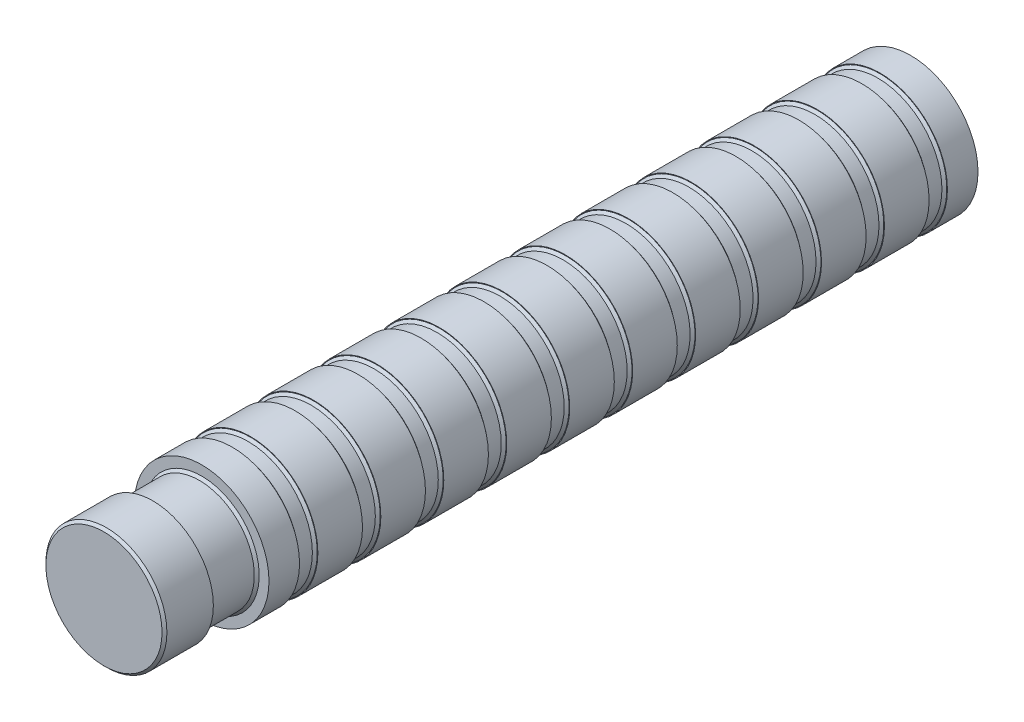
SolidWorks part; units mm, degrees
ref_plane "Front Plane" through (0, 0, 0) normal (0, 0, 1) x (1, 0, 0)
ref_plane "Top Plane" through (0, 0, 0) normal (0, 1, 0) x (1, 0, 0)
ref_plane "Right Plane" through (0, 0, 0) normal (1, 0, 0) x (0, 0, -1)
sketch "Sketch2" plane through (0, 0, 0) normal (1, 0, 0) x (0, 0, -1)
  line L0 (-29, 0) -> (29, 0)
  line L2 (-29, 5.5) -> (-26.5, 5.5)
  line L3 (29, 5.5) -> (29, 0)
  line L4 (-26.5, 5.5) -> (-26.5, 5.25)
  line L5 (-26.5, 5.25) -> (-25, 5.25)
  line L6 (-25, 5.25) -> (-25, 5.5)
  line L7 (-21.35, 5.5) -> (-21.35, 5.25)
  line L8 (-21.35, 5.25) -> (-19.85, 5.25)
  line L9 (-19.85, 5.25) -> (-19.85, 5.5)
  line L10 (-16.2, 5.5) -> (-16.2, 5.25)
  line L11 (-16.2, 5.25) -> (-14.7, 5.25)
  line L12 (-14.7, 5.25) -> (-14.7, 5.5)
  line L13 (-11.05, 5.5) -> (-11.05, 5.25)
  line L14 (-11.05, 5.25) -> (-9.55, 5.25)
  line L15 (-9.55, 5.25) -> (-9.55, 5.5)
  line L16 (-5.9, 5.5) -> (-5.9, 5.25)
  line L17 (-5.9, 5.25) -> (-4.4, 5.25)
  line L18 (-4.4, 5.25) -> (-4.4, 5.5)
  line L19 (-0.75, 5.5) -> (-0.75, 5.25)
  line L20 (-0.75, 5.25) -> (0.75, 5.25)
  line L21 (0.75, 5.25) -> (0.75, 5.5)
  line L22 (4.4, 5.5) -> (4.4, 5.25)
  line L23 (4.4, 5.25) -> (5.9, 5.25)
  line L24 (5.9, 5.25) -> (5.9, 5.5)
  line L25 (9.55, 5.5) -> (9.55, 5.25)
  line L26 (9.55, 5.25) -> (11.05, 5.25)
  line L27 (11.05, 5.25) -> (11.05, 5.5)
  line L28 (14.7, 5.5) -> (14.7, 5.25)
  line L29 (14.7, 5.25) -> (16.2, 5.25)
  line L30 (16.2, 5.25) -> (16.2, 5.5)
  line L31 (-25, 5.5) -> (-21.35, 5.5)
  line L32 (-19.85, 5.5) -> (-16.2, 5.5)
  line L33 (-14.7, 5.5) -> (-11.05, 5.5)
  line L34 (-9.55, 5.5) -> (-5.9, 5.5)
  line L35 (-4.4, 5.5) -> (-0.75, 5.5)
  line L36 (0.75, 5.5) -> (4.4, 5.5)
  line L37 (5.9, 5.5) -> (9.55, 5.5)
  line L38 (29, 0) -> (30.5762, 0) construction
  line L39 (11.05, 5.5) -> (14.7, 5.5)
  line L40 (16.2, 5.5) -> (19.85, 5.5)
  line L41 (19.85, 5.5) -> (19.85, 5.25)
  line L42 (19.85, 5.25) -> (21.35, 5.25)
  line L43 (21.35, 5.25) -> (21.35, 5.5)
  line L44 (25, 5.5) -> (25, 5.25)
  line L45 (25, 5.25) -> (26.5, 5.25)
  line L46 (26.5, 5.25) -> (26.5, 5.5)
  line L47 (21.35, 5.5) -> (25, 5.5)
  line L48 (26.5, 5.5) -> (29, 5.5)
  line L58 (-29, 5.5) -> (-29, 0)
  point P4 (0, 0)
  dimension "D1" = 58
  dimension "D2" = 2.5
  dimension "D3" = 1.5
  dimension "D4" = 0.25
  dimension "D7" = 2.5
  dimension "D8" = 3.65
  dimension "D13" = 5.5
  dimension "D6" = 11
revolve "Revolve2" add sketch "Sketch2" angle 360 about L38
sketch "Sketch3" plane through (0, 0, -29) normal (0, 0, -1) x (-1, 0, 0)
  line L0 (2.125, 0) -> (-2.125, 0) construction
  line L1 (1.475, 1.5297) -> (1.475, -1.5297)
  arc A0 (1.475, 1.5297) -> (1.475, -1.5297) centre (0, 0) ccw
  point P7 (0, 0)
  dimension "D1" = 4.25
  dimension "D2" = 3.6
extrude "Cut-Extrude1" cut sketch "Sketch3" against normal blind 14
sketch "Sketch5" plane through (0, 0, 29) normal (0, 0, 1) x (1, 0, 0)
  circle A0 centre (0, 0) radius 4.5
  dimension "D1" = 9
extrude "Boss-Extrude1" add sketch "Sketch5" along normal blind 4
sketch "Sketch6" plane through (0, 0, 33) normal (0, 0, 1) x (1, 0, 0)
  circle A0 centre (0, 0) radius 4.95
  dimension "D1" = 9.9
extrude "Boss-Extrude2" add sketch "Sketch6" along normal blind 4
chamfer "Chamfer1" distance 0.2 angle 45 25 edges at (4.95, 0, 37) (4.5, 0, 29) (4.5, 0, 33) (5.25, 0, 26.5) (5.25, 0, 25) (5.25, 0, 19.85) (5.25, 0, 21.35) (5.25, 0, -26.5) (5.25, 0, -25) (5.25, 0, -21.35) (5.25, 0, -19.85) (5.25, 0, -16.2) (5.25, 0, -14.7) (5.25, 0, -11.05) (5.25, 0, -9.55) (5.25, 0, -5.9) (5.25, 0, -4.4) (5.25, 0, -0.75) (5.25, 0, 0.75) (5.25, 0, 4.4) (5.25, 0, 5.9) (5.25, 0, 9.55) (5.25, 0, 11.05) (5.25, 0, 14.7) (5.25, 0, 16.2)
